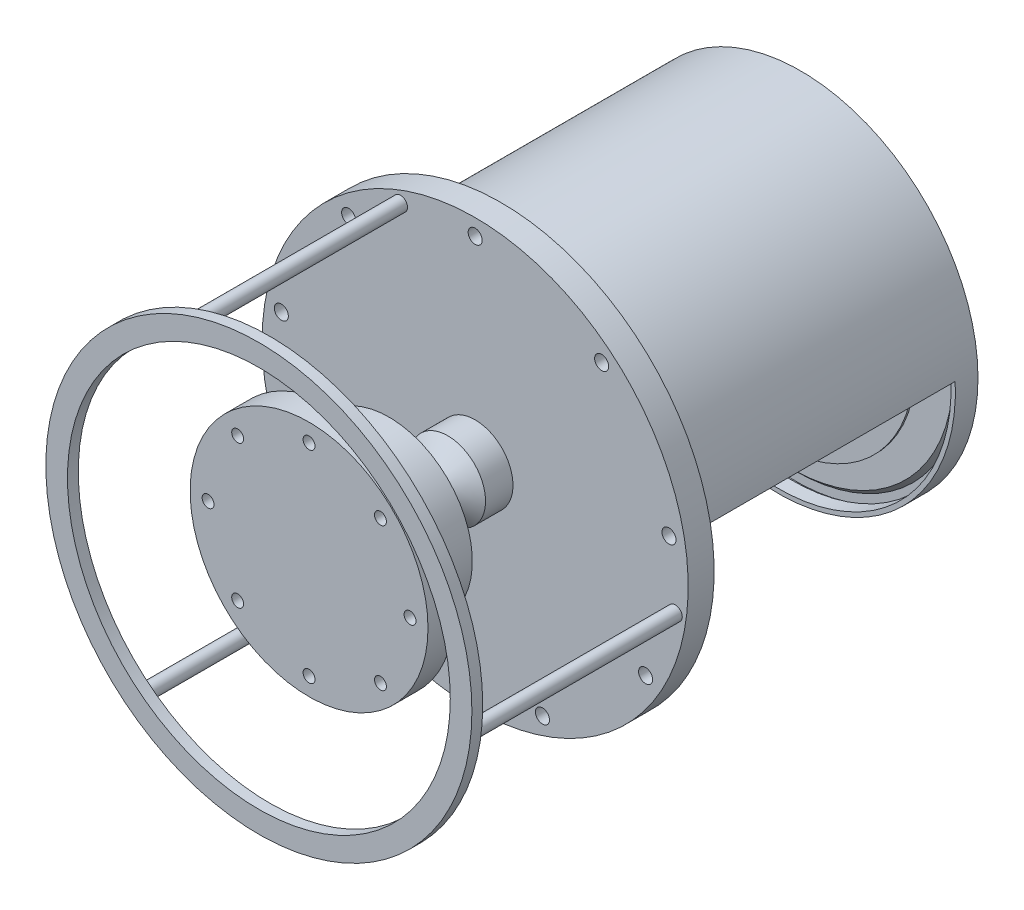
SolidWorks part; units mm, degrees
ref_plane "Front" through (0, 0, 0) normal (0, 0, 1) x (1, 0, 0)
ref_plane "Top" through (0, 0, 0) normal (0, 1, 0) x (1, 0, 0)
ref_plane "Right" through (0, 0, 0) normal (1, 0, 0) x (0, 0, -1)
sketch "Эскиз14" plane through (0, 0, 0) normal (0, 1, 0) x (1, 0, 0)
  line L0 (0, -600) -> (0, 0) construction
  line L1 (0, -441) -> (-110, -441)
  line L2 (-110, -441) -> (-110, -453)
  line L3 (-110, -453) -> (0, -453)
  line L4 (0, -441) -> (0, -453)
  dimension "D1" = 600
  dimension "D2" = 110
  dimension "D3" = 441
  dimension "D4" = 12
revolve "Повернуть11" add sketch "Эскиз14" angle 360 about L0
sketch "Эскиз15" plane through (0, 0, 0) normal (0, 1, 0) x (1, 0, 0)
  line L0 (0, 0) -> (0, -534.988) construction
  line L1 (-110, -441) -> (-110, -429)
  line L3 (-110, -441) -> (-75, -441)
  line L4 (110, -441) -> (-110, -441) construction
  line L5 (-75, -441) -> (-75, -381)
  line L6 (-75, -381) -> (-15, -381)
  line L7 (-15, -381) -> (-15, -379)
  line L8 (-110, -429) -> (-77, -429)
  line L9 (-15, -379) -> (-77, -379)
  line L10 (-77, -429) -> (-77, -379)
  dimension "D1" = 12
  dimension "D2" = 110
  dimension "D3" = 60
  dimension "D4" = 35
  dimension "D5" = 15
  dimension "D6" = 2
  dimension "D7" = 33
  dimension "D8" = 62
revolve "Повернуть12" add sketch "Эскиз15" angle 360 about L0
sketch "Эскиз16" plane through (0, 0, 0) normal (0, 1, 0) x (1, 0, 0)
  line L0 (0, 0) -> (0, -599.8085) construction
  line L1 (-15, -381) -> (-13, -381)
  line L4 (77, -379) -> (-77, -379) construction
  line L5 (-15, -381) -> (-15, -331)
  line L6 (-13, -381) -> (-13, -332.5)
  line L7 (-15, -331) -> (-13, -331)
  line L8 (-13, -332.5) -> (-11.5, -332.5)
  line L9 (-11.5, -332.5) -> (-11.5, -304.5)
  line L10 (-13, -331) -> (-13, -305.5)
  line L11 (-11.5, -304.5) -> (-18.2, -304.5)
  line L12 (-13, -305.5) -> (-15, -305.5)
  line L13 (-17.3, -307.5) -> (-15.7, -307.5)
  line L14 (-15.7, -307.5) -> (-15, -305.5)
  line L15 (-17.3, -307.5) -> (-18.2, -304.5)
  dimension "D1" = 2
  dimension "D2" = 13
  dimension "D3" = 2
  dimension "D4" = 50
  dimension "D5" = 1.5
  dimension "D6" = 1.5
  dimension "D7" = 28
  dimension "D8" = 27
  dimension "D9" = 6.7
  dimension "D10" = 2
  dimension "D11" = 2
  dimension "D12" = 4.3
  dimension "D13" = 1.6
revolve "Повернуть17" add sketch "Эскиз16" angle 360 about L0
sketch "Эскиз17" plane through (0, 0, 0) normal (0, 1, 0) x (1, 0, 0)
  line L0 (-15, -331) -> (-15, -379) construction
  line L1 (-15, -341) -> (-16.5, -341)
  line L2 (77, -379) -> (-77, -379) construction
  line L3 (-16.5, -341) -> (-16.5, -338)
  line L4 (-15, -341) -> (-15, -336.62)
  line L5 (-13, -323.4) -> (-33.5, -323.4)
  line L6 (15, -331) -> (-15, -331) construction
  line L7 (-13, -305.5) -> (-13, -331) construction
  line L8 (-15, -336.62) -> (-33.5, -323.4)
  line L9 (-16.5, -338) -> (-35, -324.78)
  line L10 (-33.5, -323.4) -> (-33.5, -283.4)
  line L11 (-35, -324.78) -> (-35, -299.4)
  line L12 (-33.5, -283.4) -> (-159.5, -283.4)
  line L13 (-159.5, -283.4) -> (-159.5, -287.4)
  line L14 (-159.5, -287.4) -> (-197, -287.4)
  line L15 (-197, -287.4) -> (-197, -299.4)
  line L16 (-197, -299.4) -> (-35, -299.4)
  line L17 (0, 0) -> (0, -530.5891) construction
  dimension "D7" = 40
  dimension "D1" = 38
  dimension "D2" = 1.5
  dimension "D3" = 3
  dimension "D4" = 4.38
  dimension "D5" = 7.6
  dimension "D6" = 20.5
  dimension "D9" = 126
  dimension "D10" = 4
  dimension "D11" = 37.5
  dimension "D12" = 12
revolve "Повернуть19" add sketch "Эскиз17" angle 360 about L17
sketch "Эскиз18" plane through (0, 0, 0) normal (0, 1, 0) x (1, 0, 0)
  line L0 (-197, -287.4) -> (-197, -275.4)
  line L1 (-197, -287.4) -> (-170, -287.4)
  line L2 (197, -287.4) -> (-197, -287.4) construction
  line L3 (-170, -287.4) -> (-170, -282.4)
  line L4 (-170, -282.4) -> (-165, -282.4)
  line L5 (-165, -282.4) -> (-165, -287.4)
  line L6 (-165, -287.4) -> (-160, -287.4)
  line L7 (-160, -287.4) -> (-160, -6.4)
  line L8 (-197, -275.4) -> (-170, -275.4)
  line L9 (-170, -275.4) -> (-170, -277.4)
  line L10 (-170, -277.4) -> (-166, -277.4)
  line L11 (-166, -277.4) -> (-166, -275.4)
  line L12 (-166, -275.4) -> (-164, -275.4)
  line L13 (-164, -275.4) -> (-164, 1.6)
  line L14 (-164, 1.6) -> (-162, 1.6)
  line L15 (-162, 1.6) -> (-162, -6.4)
  line L16 (-162, -6.4) -> (-160, -6.4)
  line L17 (0, 0) -> (0, -519.2816) construction
  dimension "D1" = 12
  dimension "D2" = 27
  dimension "D3" = 5
  dimension "D4" = 5
  dimension "D5" = 5
  dimension "D6" = 281
  dimension "D7" = 27
  dimension "D8" = 2
  dimension "D9" = 4
  dimension "D10" = 2
  dimension "D11" = 277
  dimension "D12" = 2
  dimension "D13" = 8
revolve "Повернуть20" add sketch "Эскиз18" angle 360 about L17
sketch "Эскиз19" plane through (0, 0, 0) normal (0, 1, 0) x (1, 0, 0)
  line L0 (-162, 1.6) -> (-160, 1.6)
  line L1 (162, 1.6) -> (-162, 1.6) construction
  line L2 (-162, 1.6) -> (-162, -3.4)
  line L3 (-162, 1.6) -> (-162, -6.4) construction
  line L4 (-162, -3.4) -> (-154, -3.4)
  line L5 (-160, 1.6) -> (-160, -0.4)
  line L6 (-160, -0.4) -> (-157, -0.4)
  line L7 (-157, -0.4) -> (-157, 1.6)
  line L8 (-157, 1.6) -> (-64.5, 1.6)
  line L9 (-64.5, 1.6) -> (-64.5, -0.4)
  line L10 (-64.5, -0.4) -> (-61.5, -0.4)
  line L11 (-61.5, -0.4) -> (-61.5, 1.6)
  line L12 (-61.5, 1.6) -> (-59.5, 1.6)
  line L13 (-59.5, 1.6) -> (-59.5, -0.4)
  line L14 (-59.5, -0.4) -> (-56.5, -0.4)
  line L15 (-56.5, -0.4) -> (-56.5, 1.6)
  line L16 (164, 1.6) -> (-164, 1.6) construction
  line L17 (-56.5, 1.6) -> (-30.5, 1.6)
  line L18 (-150, -7.4) -> (-25.5, -7.4)
  line L19 (-154, -3.4) -> (-150, -7.4)
  line L20 (-25.5, -7.4) -> (-25.5, -6.4)
  line L21 (-25.5, -6.4) -> (-30.5, 1.6)
  line L22 (0, 0) -> (0, -521.8345) construction
  dimension "D1" = 2
  dimension "D2" = 5
  dimension "D3" = 8
  dimension "D4" = 2
  dimension "D5" = 3
  dimension "D6" = 92.5
  dimension "D7" = 2
  dimension "D8" = 3
  dimension "D9" = 2
  dimension "D10" = 2
  dimension "D11" = 3
  dimension "D12" = 26
  dimension "D13" = 9
  dimension "D14" = 12
  dimension "D15" = 124.5
  dimension "D16" = 1
revolve "Повернуть21" add sketch "Эскиз19" angle 360 about L22
sketch "Эскиз20" plane through (0, 0, 0) normal (0, 1, 0) x (1, 0, 0)
  line L0 (0, 0) -> (0, -558.111) construction
  line L1 (-156.5, -243.4) -> (-12.5, -243.4)
  line L2 (197, -275.4) -> (-197, -275.4) construction
  line L3 (-160, -6.4) -> (-160, -287.4) construction
  line L4 (-12.5, -243.4) -> (-12.5, -227.4)
  line L5 (-12.5, -227.4) -> (-14.5, -227.4)
  line L6 (-14.5, -227.4) -> (-14.5, -229.4)
  line L7 (-14.5, -229.4) -> (-16.5, -229.4)
  line L8 (-16.5, -229.4) -> (-16.5, -227.4)
  line L9 (-16.5, -227.4) -> (-119.5, -227.4)
  line L10 (-119.5, -227.4) -> (-119.5, -233.4)
  line L11 (-119.5, -233.4) -> (-130.5, -233.4)
  line L12 (-130.5, -233.4) -> (-130.5, -230.4)
  line L13 (-130.5, -230.4) -> (-136.5, -230.4)
  line L14 (-136.5, -230.4) -> (-136.5, -233.4)
  line L15 (-136.5, -233.4) -> (-156.5, -233.4)
  line L16 (-156.5, -233.4) -> (-156.5, -243.4)
  dimension "D1" = 32
  dimension "D2" = 3.5
  dimension "D3" = 144
  dimension "D4" = 16
  dimension "D5" = 2
  dimension "D6" = 2
  dimension "D7" = 2
  dimension "D8" = 2
  dimension "D9" = 103
  dimension "D10" = 6
  dimension "D11" = 11
  dimension "D12" = 3
  dimension "D13" = 6
  dimension "D14" = 20
  dimension "D15" = 3
revolve "Повернуть22" add sketch "Эскиз20" angle 360 about L0
sketch "Эскиз21" plane through (0, 0, 0) normal (0, 1, 0) x (1, 0, 0)
  line L0 (-16.5, -307.5) -> (-16.5, -301.5)
  line L1 (-17.3, -307.5) -> (17.3, -307.5) construction
  line L2 (-16.5, -301.5) -> (-19.5, -301.5)
  line L3 (-19.5, -301.5) -> (-19.5, -253.5)
  line L4 (-19.5, -253.5) -> (-16.5, -253.5)
  line L5 (-16.5, -253.5) -> (-16.5, -251)
  line L6 (-17, -301.5) -> (-18.479, -300.5)
  line L7 (-18.479, -300.5) -> (-17, -299.9062)
  line L8 (-17, -299.91) -> (-18.479, -298.91)
  line L9 (-18.479, -298.91) -> (-17, -298.3162)
  line L10 (-17, -298.32) -> (-18.479, -297.32)
  line L11 (-18.479, -297.32) -> (-17, -296.7262)
  line L12 (-17, -296.73) -> (-18.479, -295.73)
  line L13 (-18.479, -295.73) -> (-17, -295.1362)
  line L14 (-17, -295.14) -> (-18.479, -294.14)
  line L15 (-18.479, -294.14) -> (-17, -293.5462)
  line L16 (-17, -293.55) -> (-18.479, -292.55)
  line L17 (-18.479, -292.55) -> (-17, -291.9562)
  line L18 (-17, -291.96) -> (-18.479, -290.96)
  line L19 (-18.479, -290.96) -> (-17, -290.3662)
  line L20 (-17, -290.37) -> (-18.479, -289.37)
  line L21 (-18.479, -289.37) -> (-17, -288.7762)
  line L22 (-17, -288.78) -> (-18.479, -287.78)
  line L23 (-18.479, -287.78) -> (-17, -287.1862)
  line L24 (-17, -287.19) -> (-18.479, -286.19)
  line L25 (-18.479, -286.19) -> (-17, -285.5962)
  line L26 (-17, -285.6) -> (-18.479, -284.6)
  line L27 (-18.479, -284.6) -> (-17, -284.0062)
  line L28 (-17, -284.01) -> (-18.479, -283.01)
  line L29 (-18.479, -283.01) -> (-17, -282.4162)
  line L30 (-17, -282.42) -> (-18.479, -281.42)
  line L31 (-18.479, -281.42) -> (-17, -280.8262)
  line L32 (-17, -280.83) -> (-18.479, -279.83)
  line L33 (-18.479, -279.83) -> (-17, -279.2362)
  line L34 (-17, -279.24) -> (-18.479, -278.24)
  line L35 (-18.479, -278.24) -> (-17, -277.6462)
  line L36 (-17, -277.65) -> (-18.479, -276.65)
  line L37 (-18.479, -276.65) -> (-17, -276.0562)
  line L38 (-17, -276.06) -> (-18.479, -275.06)
  line L39 (-18.479, -275.06) -> (-17, -274.4662)
  line L40 (-17, -274.47) -> (-18.479, -273.47)
  line L41 (-18.479, -273.47) -> (-17, -272.8762)
  line L42 (-17, -272.88) -> (-18.479, -271.88)
  line L43 (-18.479, -271.88) -> (-17, -271.2862)
  line L44 (-17, -271.29) -> (-18.479, -270.29)
  line L45 (-18.479, -270.29) -> (-17, -269.6962)
  line L46 (-17, -269.7) -> (-18.479, -268.7)
  line L47 (-18.479, -268.7) -> (-17, -268.1062)
  line L48 (-17, -268.11) -> (-18.479, -267.11)
  line L49 (-18.479, -267.11) -> (-17, -266.5162)
  line L50 (-17, -266.52) -> (-18.479, -265.52)
  line L51 (-18.479, -265.52) -> (-17, -264.9262)
  line L52 (-17, -264.93) -> (-18.479, -263.93)
  line L53 (-18.479, -263.93) -> (-17, -263.3362)
  line L54 (-17, -263.34) -> (-18.479, -262.34)
  line L55 (-18.479, -262.34) -> (-17, -261.7462)
  line L56 (-17, -261.75) -> (-18.479, -260.75)
  line L57 (-18.479, -260.75) -> (-17, -260.1562)
  line L58 (-17, -260.16) -> (-18.479, -259.16)
  line L59 (-18.479, -259.16) -> (-17, -258.5662)
  line L60 (-17, -258.57) -> (-18.479, -257.57)
  line L61 (-18.479, -257.57) -> (-17, -256.9762)
  line L62 (-17, -256.98) -> (-18.479, -255.98)
  line L63 (-18.479, -255.98) -> (-17, -255.3862)
  line L64 (-17, -255.39) -> (-18.479, -254.39)
  line L65 (-18.479, -254.39) -> (-17, -253.7962)
  line L66 (-17, -253.7962) -> (-17, -253.5)
  line L67 (-18.2, -251) -> (-10.2, -251)
  line L68 (-16.5, -251) -> (-16.5, -247.5)
  line L69 (-10.2, -251) -> (-10.2, -227.4)
  line L70 (119.5, -227.4) -> (-119.5, -227.4) construction
  line L71 (-10.2, -227.4) -> (-12.5, -227.4)
  line L72 (12.5, -227.4) -> (-12.5, -227.4) construction
  line L73 (-12.5, -227.4) -> (-12.5, -250)
  line L74 (-12.5, -250) -> (-15.03, -250)
  line L75 (-16.5, -247.5) -> (-17.3, -247.5)
  line L76 (-16.5, -247.5) -> (-15.7, -247.5)
  line L77 (-17.3, -247.5) -> (-18.2, -251)
  line L78 (-15.7, -247.5) -> (-15.03, -250)
  line L79 (0, 0) -> (0, -502.5003) construction
  dimension "D1" = 0.8
  dimension "D2" = 8
  dimension "D3" = 1.7
  dimension "D4" = 48
  dimension "D5" = 3
  dimension "D6" = 2.5
  dimension "D7" = 1
  dimension "D8" = 2.5
  dimension "D9" = 1.5938
  dimension "D11" = 3.5
  dimension "D12" = 1
  dimension "D13" = 2.53
  dimension "D14" = 0.8
  dimension "D15" = 0.8
  dimension "D10" = 30
revolve "Повернуть26" add sketch "Эскиз21" angle 360 about L79
sketch "Эскиз22" plane through (0, 0, 0) normal (0, 1, 0) x (1, 0, 0)
  line L0 (-156.5, -232.4) -> (-136.5, -232.4)
  line L1 (156.5, -233.4) -> (-156.5, -233.4) construction
  line L2 (-136.5, -230.4) -> (-136.5, -233.4) construction
  line L3 (-156.5, -232.4) -> (-156.5, -216.4)
  line L4 (-156.5, -216.4) -> (-123.5, -216.4)
  line L5 (-123.5, -216.4) -> (-123.5, -19.4)
  line L6 (-123.5, -19.4) -> (-121.75, -19.4)
  line L7 (-121.75, -19.4) -> (-121.75, -20.9)
  line L8 (-121.75, -20.9) -> (-120.5, -20.9)
  line L9 (-120.5, -20.9) -> (-120.5, -229.4)
  line L10 (-120.5, -229.4) -> (-123.9, -229.4)
  line L11 (-123.9, -229.4) -> (-127.56, -224.4)
  line L12 (-127.56, -224.4) -> (-130.82, -224.4)
  line L13 (-130.82, -224.4) -> (-130.82, -230.4)
  line L14 (-136.5, -232.4) -> (-136.5, -230.4)
  line L15 (-136.5, -230.4) -> (-130.82, -230.4)
  line L16 (0, 0) -> (0, -544.1149) construction
  dimension "D1" = 1
  dimension "D2" = 16
  dimension "D3" = 33
  dimension "D4" = 197
  dimension "D5" = 1.75
  dimension "D6" = 1.5
  dimension "D7" = 1.25
  dimension "D8" = 208.5
  dimension "D9" = 3.4
  dimension "D10" = 5
  dimension "D11" = 3.26
  dimension "D12" = 6
revolve "Повернуть27" add sketch "Эскиз22" angle 360 about L16
sketch "Эскиз23" plane through (0, 0, 0) normal (0, 1, 0) x (1, 0, 0)
  line L0 (-125.5, -204.4) -> (-125.5, -17.4)
  line L1 (156.5, -216.4) -> (-156.5, -216.4) construction
  line L2 (-123.5, -19.4) -> (-123.5, -216.4) construction
  line L3 (-125.5, -17.4) -> (0, -17.4)
  line L4 (0, 0) -> (0, -784.7245) construction
  line L5 (-125.5, -204.4) -> (-123.5, -204.4)
  line L6 (-123.5, -204.4) -> (-123.5, -19.4)
  line L7 (123.5, -19.4) -> (-123.5, -19.4) construction
  line L8 (-123.5, -19.4) -> (0, -19.4)
  line L9 (121.75, -19.4) -> (-121.75, -19.4) construction
  line L10 (0, -19.4) -> (0, -17.4)
  dimension "D1" = 12
  dimension "D2" = 2
  dimension "D3" = 187
  dimension "D5" = 2
revolve "Медная рубашка" add sketch "Эскиз23" angle 360 about L4
sketch "отверсия под болты" plane through (0, 0, 275.4) normal (0, 0, -1) x (-1, 0, 0)
  circle A0 centre (0, 182) radius 6.5
  circle A1 centre (116.9873, 139.4201) radius 6.5
  circle A2 centre (179.235, 31.604) radius 6.5
  circle A3 centre (157.6166, -91) radius 6.5
  circle A4 centre (62.2477, -171.0241) radius 6.5
  circle A5 centre (-62.2477, -171.0241) radius 6.5
  circle A6 centre (-157.6166, -91) radius 6.5
  circle A7 centre (-179.235, 31.604) radius 6.5
  circle A8 centre (-116.9873, 139.4201) radius 6.5
  point P21 (0, 0)
  dimension "D1" = 9
extrude "Вырез-Вытянуть2" cut sketch "отверсия под болты" against normal blind 34
sketch "Эскиз24" plane through (0, 0, 453) normal (0, 0, 1) x (1, 0, 0)
  circle A0 centre (0, 93.3932) radius 5.5
  circle A1 centre (66.039, 66.039) radius 5.5
  circle A2 centre (93.3932, 0) radius 5.5
  circle A3 centre (66.039, -66.039) radius 5.5
  circle A4 centre (0, -93.3932) radius 5.5
  circle A5 centre (-66.039, -66.039) radius 5.5
  circle A6 centre (-93.3932, 0) radius 5.5
  circle A7 centre (-66.039, 66.039) radius 5.5
  point P20 (0, 0)
  dimension "D1" = 8
extrude "Вырез-Вытянуть3" cut sketch "Эскиз24" against normal up to surface (24 mm away) up to face at (-110, 0, 429)
sketch "Эскиз26" plane through (0, 0, 299.4) normal (0, 0, 1) x (1, 0, 0)
  circle A0 centre (-115.9758, -146.6922) radius 6.5
  circle A2 centre (-69.0513, 173.7841) radius 6.5
  circle A3 centre (185.0271, -27.0919) radius 6.5
  point P9 (0, 0)
  dimension "D1" = 187
  dimension "D2" = 3
extrude "Бобышка-Вытянуть1" add sketch "Эскиз26" along normal blind 190
sketch "Эскиз27" plane through (0, 0, 489.4) normal (0, 0, 1) x (1, 0, 0)
  circle A0 centre (0, 0) radius 197
  circle A1 centre (0, 0) radius 177
extrude "Бобышка-Вытянуть2" add sketch "Эскиз27" along normal blind 10
extrude "Вырез-Вытянуть4" cut sketch "Эскиз28" against normal blind 250
sketch "Эскиз28" plane through (0.5052, -2.8714, -1.6) normal (-0.0642, 0.9979, 0) x (0.9979, 0.0642, 0)
  line L1 (-266.4075, -252.9841) -> (389.9777, -252.9841)
  line L2 (-266.4075, -252.9841) -> (-266.4075, -20.8806)
  line L3 (-266.4075, -20.8806) -> (389.9777, -20.8806)
  line L4 (389.9777, -252.9841) -> (389.9777, -20.8806)
